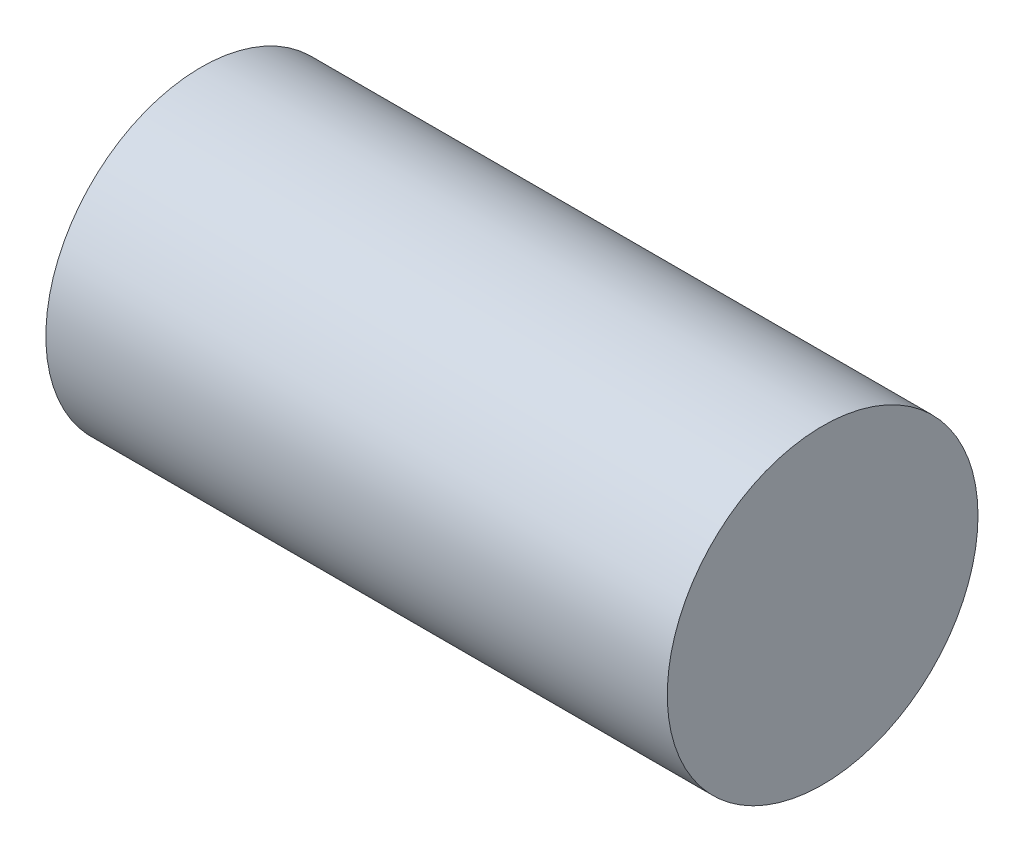
SolidWorks part; units mm, degrees
material " PFA-440HP"
ref_plane "Front" through (0, 0, 0) normal (0, 0, 1) x (1, 0, 0)
ref_plane "Top" through (0, 0, 0) normal (0, 1, 0) x (1, 0, 0)
ref_plane "Right" through (0, 0, 0) normal (1, 0, 0) x (0, 0, -1)
sketch "Sketch1" plane through (0, 0, 0) normal (1, 0, 0) x (0, 0, -1)
  circle A0 centre (0, 0) radius 2.5
  dimension "D1" = 5
extrude "Extrude1" add sketch "Sketch1" along normal blind 10
